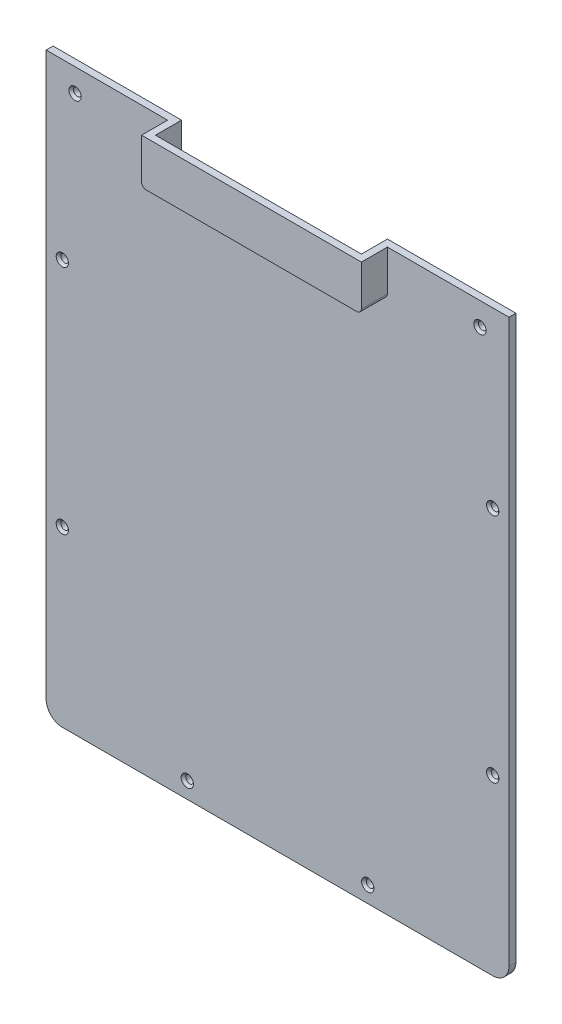
SolidWorks part; units mm, degrees
ref_plane "Front" through (0, 0, 0) normal (0, 0, 1) x (1, 0, 0)
ref_plane "Top" through (0, 0, 0) normal (0, 1, 0) x (1, 0, 0)
ref_plane "Right" through (0, 0, 0) normal (1, 0, 0) x (0, 0, -1)
sketch "Sketch1" plane through (0, 0, 0) normal (0, 0, 1) x (1, 0, 0)
  line L0 (200, 250) -> (200, 7) construction
  line L1 (0, 0) -> (200, 0)
  line L2 (0, 0) -> (0, 250)
  line L3 (0, 250) -> (200, 250)
  line L4 (200, 0) -> (200, 250)
  line L5 (195, 250) -> (180, 250) construction
extrude "Boss-Extrude1" add sketch "Sketch1" along normal blind 3
fillet "Fillet1" radius 7 2 edges at (0, 0, 1.5) (200, 0, 1.5)
sketch "Sketch2" plane through (0, 0, 0) normal (0, 0, 1) x (1, 0, 0)
  line L0 (100, 250) -> (100, 0) construction
  line L1 (210, 250) -> (-10, 250) construction
  line L2 (7, 0) -> (193, 0) construction
  line L3 (57.5, 253) -> (57.5, 251.5) construction
  line L4 (144.5, 233.5) -> (55.5, 233.5)
  line L5 (144.5, 233.5) -> (144.5, 250)
  line L6 (144.5, 250) -> (55.5, 250)
  line L7 (55.5, 233.5) -> (55.5, 250)
  line L8 (144.5, 233.5) -> (55.5, 250) construction
  line L9 (144.5, 250) -> (55.5, 233.5) construction
  line L10 (85.25, 236.5) -> (94.5, 236.5) construction
  point P6 (100, 241.75)
  dimension "D1" = 2
  dimension "D2" = 3
extrude "Cut-Extrude2" cut sketch "Sketch2" along normal up to surface (3 mm away) up to face at (100, 85.1834, 3)
sketch "Sketch3" plane through (0, 0, 3) normal (0, 0, 1) x (1, 0, 0)
  line L0 (144.5, 250) -> (144.5, 233.5) construction
  line L1 (55.5, 233.5) -> (55.5, 250) construction
  line L2 (144.5, 233.5) -> (55.5, 233.5) construction
  line L3 (144.5, 250) -> (144.5, 233.5)
  line L4 (55.5, 233.5) -> (55.5, 250)
  line L5 (144.5, 233.5) -> (55.5, 233.5)
extrude "Extrude-Thin1" add sketch "Sketch3" along normal up to vertex (8.25 mm away) thin thin type one direction reverse wall 3
sketch "Sketch4" plane through (0, 0, 11.25) normal (0, 0, 1) x (1, 0, 0)
  line L1 (52.5, 250) -> (147.5, 250)
  line L2 (52.5, 250) -> (52.5, 230.5)
  line L3 (52.5, 230.5) -> (147.5, 230.5)
  line L4 (147.5, 250) -> (147.5, 230.5)
extrude "Boss-Extrude2" add sketch "Sketch4" along normal blind 3
fillet "Fillet2" radius 2 2 edges at (55.5, 233.5, 5.625) (144.5, 233.5, 5.625)
fillet "Fillet3" radius 2 2 edges at (147.5, 230.5, 8.625) (52.5, 230.5, 8.625)
sketch "Sketch5" plane through (0, 0, 3) normal (0, 0, 1) x (1, 0, 0)
  circle A0 centre (12.5, 240) radius 1.65
  circle A1 centre (187.5, 240) radius 1.65
  circle A2 centre (7, 175) radius 1.65
  circle A3 centre (7, 75) radius 1.65
  circle A4 centre (61, 7) radius 1.65
  circle A5 centre (139, 7) radius 1.65
  circle A6 centre (193, 175) radius 1.65
  circle A7 centre (193, 75) radius 1.65
  circle A8 centre (7, 75) radius 1.25 construction
  circle A9 centre (61, 7) radius 1.25 construction
  circle A10 centre (139, 7) radius 1.25 construction
  circle A11 centre (193, 75) radius 1.25 construction
  circle A12 centre (193, 175) radius 1.25 construction
  circle A13 centre (187.5, 240) radius 1.25 construction
  circle A14 centre (12.5, 240) radius 1.25 construction
  circle A15 centre (7, 175) radius 1.25 construction
  dimension "D1" = 3.3
extrude "Cut-Extrude3" cut sketch "Sketch5" against normal through all
chamfer "Chamfer1" distance 1 angle 45 8 edges at (62.65, 7, 3) (140.65, 7, 3) (194.65, 75, 3) (8.65, 75, 3) (8.65, 175, 3) (14.15, 240, 3) (189.15, 240, 3) (194.65, 175, 3)
